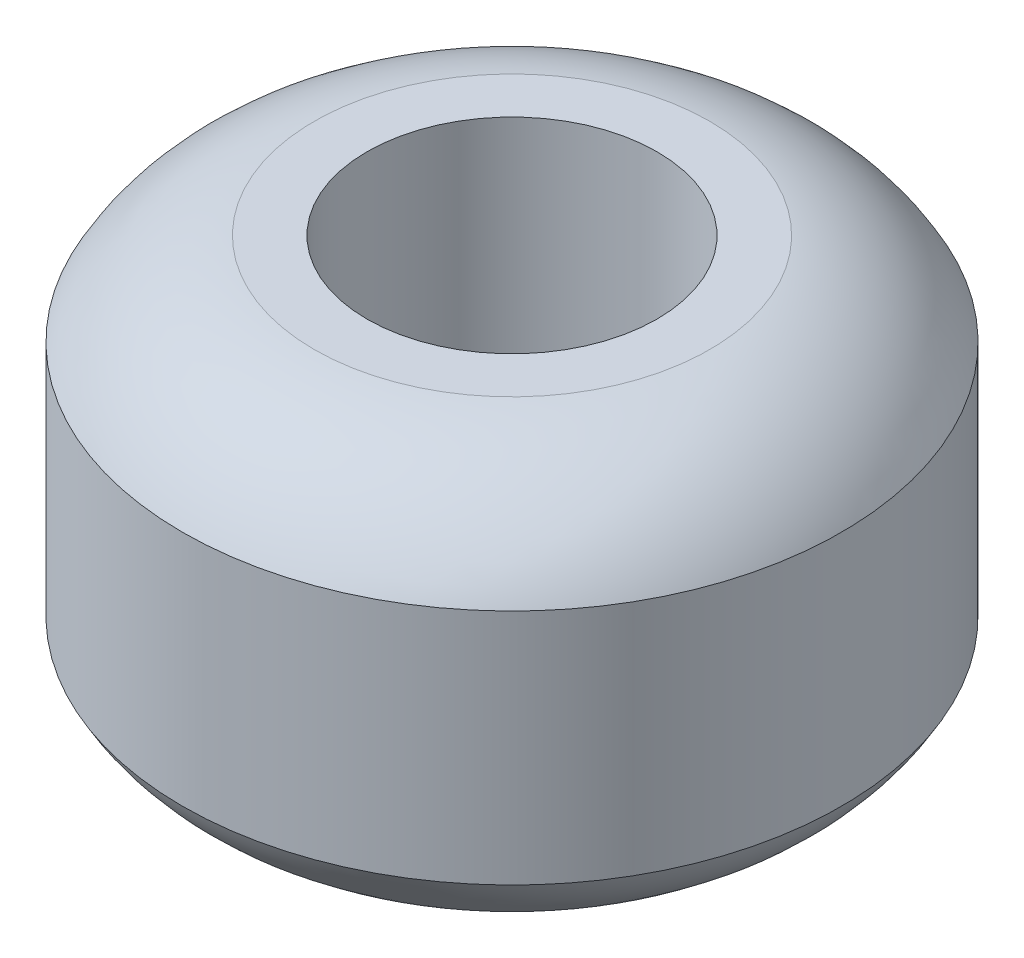
SolidWorks part; units mm, degrees
ref_plane "Front Plane" through (0, 0, 0) normal (0, 0, 1) x (1, 0, 0)
ref_plane "Top Plane" through (0, 0, 0) normal (0, 1, 0) x (1, 0, 0)
ref_plane "Right Plane" through (0, 0, 0) normal (1, 0, 0) x (0, 0, -1)
sketch "Sketch2" plane through (0, 0, 0) normal (0, 0, 1) x (1, 0, 0)
  line L0 (11, 16) -> (11, -16)
  line L1 (11, -16) -> (15, -16)
  line L2 (25, 9) -> (25, -9)
  line L3 (11, 0) -> (25, 0) construction
  line L4 (0, 0) -> (0, -29.5844) construction
  line L5 (11, 16) -> (15, 16)
  arc A1 (15, -16) -> (25, -9) centre (13.0802, -2.6146) ccw
  arc A2 (15, 16) -> (25, 9) centre (13.0802, 2.6146) cw
  dimension "D6" = 7
  dimension "D1" = 25
  dimension "D2" = 11
  dimension "D3" = 4
  dimension "D4" = 16
  dimension "D5" = 9
  dimension "D7" = 14
sketch "Sketch3" plane through (0, 0, 0) normal (0, 0, 1) x (1, 0, 0)
revolve "Revolve1" add sketch "Sketch2" angle 360 about L4
